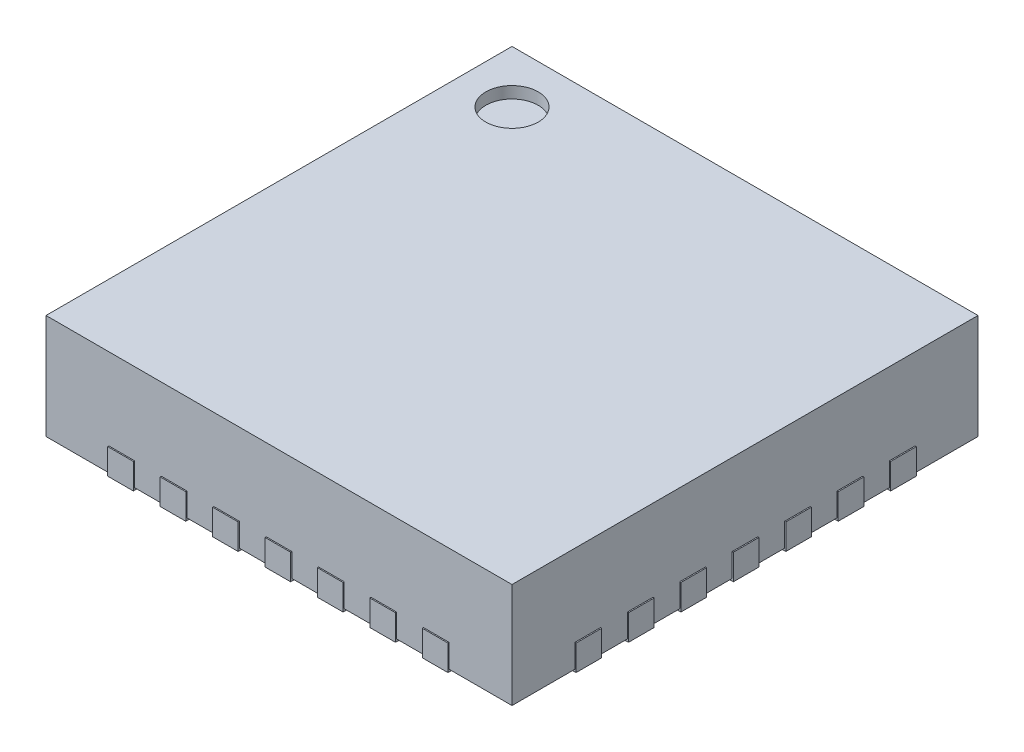
SolidWorks part; units mm, degrees
ref_plane "Front Plane" through (0, 0, 0) normal (0, 0, 1) x (1, 0, 0)
ref_plane "Top Plane" through (0, 0, 0) normal (0, 1, 0) x (1, 0, 0)
ref_plane "Right Plane" through (0, 0, 0) normal (1, 0, 0) x (0, 0, -1)
sketch "Sketch2" plane through (0, 0, 0) normal (0, 1, 0) x (1, 0, 0)
  line L1 (-2, -2) -> (2, -2)
  line L2 (-2, -2) -> (-2, 2)
  line L3 (-2, 2) -> (2, 2)
  line L4 (2, -2) -> (2, 2)
  line L5 (-2, -2) -> (2, 2) construction
  line L6 (-2, 2) -> (2, -2) construction
  point P0 (0, 0)
  dimension "D1" = 4
  dimension "D2" = 4
extrude "Boss-Extrude1" add sketch "Sketch2" along normal blind 0.9
sketch "Sketch3" plane through (0, 0, 0) normal (0, -1, 0) x (1, 0, 0)
  line L1 (-1.2, -1.2) -> (1.2, -1.2)
  line L2 (-1.2, -1.2) -> (-1.2, 1.2)
  line L3 (-1.2, 1.2) -> (1.2, 1.2)
  line L4 (1.2, -1.2) -> (1.2, 1.2)
  line L5 (-1.2, -1.2) -> (1.2, 1.2) construction
  line L6 (-1.2, 1.2) -> (1.2, -1.2) construction
  line L16 (2, 0) -> (-2, 0) construction
  line L17 (2, 2) -> (2, -2) construction
  line L18 (-2, -2) -> (-2, 2) construction
  line L19 (0, 2) -> (0, -2) construction
  line L20 (-2, 2) -> (2, 2) construction
  line L21 (2, -2) -> (-2, -2) construction
  line L22 (-1.61, 0.34) -> (-1.61, 0.56)
  line L23 (-1.61, -0.11) -> (-2.01, -0.11)
  line L24 (-1.61, -0.11) -> (-1.61, 0.11)
  line L25 (-1.61, 0.11) -> (-2.01, 0.11)
  line L26 (-2.01, -0.11) -> (-2.01, 0.11)
  line L27 (-1.61, -0.11) -> (-2.01, 0.11) construction
  line L28 (-1.61, 0.11) -> (-2.01, -0.11) construction
  line L29 (-1.61, 0.34) -> (-2.01, 0.34)
  line L30 (-2.01, 0.34) -> (-2.01, 0.56)
  line L31 (-1.61, 0.56) -> (-2.01, 0.56)
  line L32 (-1.61, 0.79) -> (-1.61, 1.01)
  line L33 (-1.61, 0.79) -> (-2.01, 0.79)
  line L34 (-2.01, 0.79) -> (-2.01, 1.01)
  line L35 (-1.61, 1.01) -> (-2.01, 1.01)
  line L36 (-1.61, 1.24) -> (-1.61, 1.46)
  line L37 (-1.61, 1.24) -> (-2.01, 1.24)
  line L38 (-2.01, 1.24) -> (-2.01, 1.46)
  line L39 (-1.61, 1.46) -> (-2.01, 1.46)
  line L40 (-1.61, -0.56) -> (-1.61, -0.34)
  line L41 (-1.61, -0.56) -> (-2.01, -0.56)
  line L42 (-2.01, -0.56) -> (-2.01, -0.34)
  line L43 (-1.61, -0.34) -> (-2.01, -0.34)
  line L44 (-1.61, -1.01) -> (-1.61, -0.79)
  line L45 (-1.61, -1.01) -> (-2.01, -1.01)
  line L46 (-2.01, -1.01) -> (-2.01, -0.79)
  line L47 (-1.61, -0.79) -> (-2.01, -0.79)
  line L48 (-1.61, -1.46) -> (-1.61, -1.24)
  line L49 (-1.61, -1.46) -> (-2.01, -1.46)
  line L50 (-2.01, -1.46) -> (-2.01, -1.24)
  line L51 (-1.61, -1.24) -> (-2.01, -1.24)
  line L52 (0.34, 1.61) -> (0.56, 1.61)
  line L53 (-0.11, 1.61) -> (-0.11, 2.01)
  line L54 (-0.11, 1.61) -> (0.11, 1.61)
  line L55 (0.11, 1.61) -> (0.11, 2.01)
  line L56 (-0.11, 2.01) -> (0.11, 2.01)
  line L57 (0.34, 1.61) -> (0.34, 2.01)
  line L58 (0.34, 2.01) -> (0.56, 2.01)
  line L59 (0.56, 1.61) -> (0.56, 2.01)
  line L60 (0.79, 1.61) -> (1.01, 1.61)
  line L61 (0.79, 1.61) -> (0.79, 2.01)
  line L62 (0.79, 2.01) -> (1.01, 2.01)
  line L63 (1.01, 1.61) -> (1.01, 2.01)
  line L64 (1.24, 1.61) -> (1.46, 1.61)
  line L65 (1.24, 1.61) -> (1.24, 2.01)
  line L66 (1.24, 2.01) -> (1.46, 2.01)
  line L67 (1.46, 1.61) -> (1.46, 2.01)
  line L68 (-0.56, 1.61) -> (-0.34, 1.61)
  line L69 (-0.56, 1.61) -> (-0.56, 2.01)
  line L70 (-0.56, 2.01) -> (-0.34, 2.01)
  line L71 (-0.34, 1.61) -> (-0.34, 2.01)
  line L72 (-1.01, 1.61) -> (-0.79, 1.61)
  line L73 (-1.01, 1.61) -> (-1.01, 2.01)
  line L74 (-1.01, 2.01) -> (-0.79, 2.01)
  line L75 (-0.79, 1.61) -> (-0.79, 2.01)
  line L76 (-1.46, 1.61) -> (-1.24, 1.61)
  line L77 (-1.46, 1.61) -> (-1.46, 2.01)
  line L78 (-1.46, 2.01) -> (-1.24, 2.01)
  line L79 (-1.24, 1.61) -> (-1.24, 2.01)
  line L80 (-0.11, 1.61) -> (0.11, 2.01) construction
  line L81 (0.11, 1.61) -> (-0.11, 2.01) construction
  line L82 (1.61, -0.34) -> (1.61, -0.56)
  line L83 (1.61, 0.11) -> (2.01, 0.11)
  line L84 (1.61, 0.11) -> (1.61, -0.11)
  line L85 (1.61, -0.11) -> (2.01, -0.11)
  line L86 (2.01, 0.11) -> (2.01, -0.11)
  line L87 (1.61, -0.34) -> (2.01, -0.34)
  line L88 (2.01, -0.34) -> (2.01, -0.56)
  line L89 (1.61, -0.56) -> (2.01, -0.56)
  line L90 (1.61, -0.79) -> (1.61, -1.01)
  line L91 (1.61, -0.79) -> (2.01, -0.79)
  line L92 (2.01, -0.79) -> (2.01, -1.01)
  line L93 (1.61, -1.01) -> (2.01, -1.01)
  line L94 (1.61, -1.24) -> (1.61, -1.46)
  line L95 (1.61, -1.24) -> (2.01, -1.24)
  line L96 (2.01, -1.24) -> (2.01, -1.46)
  line L97 (1.61, -1.46) -> (2.01, -1.46)
  line L98 (1.61, 0.56) -> (1.61, 0.34)
  line L99 (1.61, 0.56) -> (2.01, 0.56)
  line L100 (2.01, 0.56) -> (2.01, 0.34)
  line L101 (1.61, 0.34) -> (2.01, 0.34)
  line L102 (1.61, 1.01) -> (1.61, 0.79)
  line L103 (1.61, 1.01) -> (2.01, 1.01)
  line L104 (2.01, 1.01) -> (2.01, 0.79)
  line L105 (1.61, 0.79) -> (2.01, 0.79)
  line L106 (1.61, 1.46) -> (1.61, 1.24)
  line L107 (1.61, 1.46) -> (2.01, 1.46)
  line L108 (2.01, 1.46) -> (2.01, 1.24)
  line L109 (1.61, 1.24) -> (2.01, 1.24)
  line L110 (1.61, 0.11) -> (2.01, -0.11) construction
  line L111 (1.61, -0.11) -> (2.01, 0.11) construction
  line L112 (-0.34, -1.61) -> (-0.56, -1.61)
  line L113 (0.11, -1.61) -> (0.11, -2.01)
  line L114 (0.11, -1.61) -> (-0.11, -1.61)
  line L115 (-0.11, -1.61) -> (-0.11, -2.01)
  line L116 (0.11, -2.01) -> (-0.11, -2.01)
  line L117 (-0.34, -1.61) -> (-0.34, -2.01)
  line L118 (-0.34, -2.01) -> (-0.56, -2.01)
  line L119 (-0.56, -1.61) -> (-0.56, -2.01)
  line L120 (-0.79, -1.61) -> (-1.01, -1.61)
  line L121 (-0.79, -1.61) -> (-0.79, -2.01)
  line L122 (-0.79, -2.01) -> (-1.01, -2.01)
  line L123 (-1.01, -1.61) -> (-1.01, -2.01)
  line L124 (-1.24, -1.61) -> (-1.46, -1.61)
  line L125 (-1.24, -1.61) -> (-1.24, -2.01)
  line L126 (-1.24, -2.01) -> (-1.46, -2.01)
  line L127 (-1.46, -1.61) -> (-1.46, -2.01)
  line L128 (0.56, -1.61) -> (0.34, -1.61)
  line L129 (0.56, -1.61) -> (0.56, -2.01)
  line L130 (0.56, -2.01) -> (0.34, -2.01)
  line L131 (0.34, -1.61) -> (0.34, -2.01)
  line L132 (1.01, -1.61) -> (0.79, -1.61)
  line L133 (1.01, -1.61) -> (1.01, -2.01)
  line L134 (1.01, -2.01) -> (0.79, -2.01)
  line L135 (0.79, -1.61) -> (0.79, -2.01)
  line L136 (1.46, -1.61) -> (1.24, -1.61)
  line L137 (1.46, -1.61) -> (1.46, -2.01)
  line L138 (1.46, -2.01) -> (1.24, -2.01)
  line L139 (1.24, -1.61) -> (1.24, -2.01)
  line L140 (0.11, -1.61) -> (-0.11, -2.01) construction
  line L141 (-0.11, -1.61) -> (0.11, -2.01) construction
  point P0 (0, 0)
  point P18 (-1.81, 0)
  point P50 (0, 1.81)
  point P79 (1.81, 0)
  point P108 (0, -1.81)
  point P137 (0, 0)
  dimension "D1" = 2.4
  dimension "D2" = 2.4
  dimension "D3" = 0.01
  dimension "D4" = 0.4
  dimension "D5" = 0.22
  dimension "D7" = 0.23
  dimension "D9" = 0.23
  dimension "D11" = 1.61
  dimension "D12" = 0.54
  dimension "D6" = 4
  dimension "D8" = 4
  dimension "D10" = 4
extrude "Boss-Extrude2" add sketch "Sketch3" along normal blind 0.02 and the other way blind 0.2 separate body
sketch "Sketch4" plane through (0, 0.9, 0) normal (0, 1, 0) x (1, 0, 0)
  line L0 (2, 2) -> (-2, 2) construction
  line L1 (-2, 2) -> (-2, -2) construction
  circle A0 centre (-1.55, 1.55) radius 0.225
  dimension "D1" = 0.45
  dimension "D2" = 0.45
  dimension "D3" = 0.45
extrude "Cut-Extrude1" cut sketch "Sketch4" against normal blind 0.1
